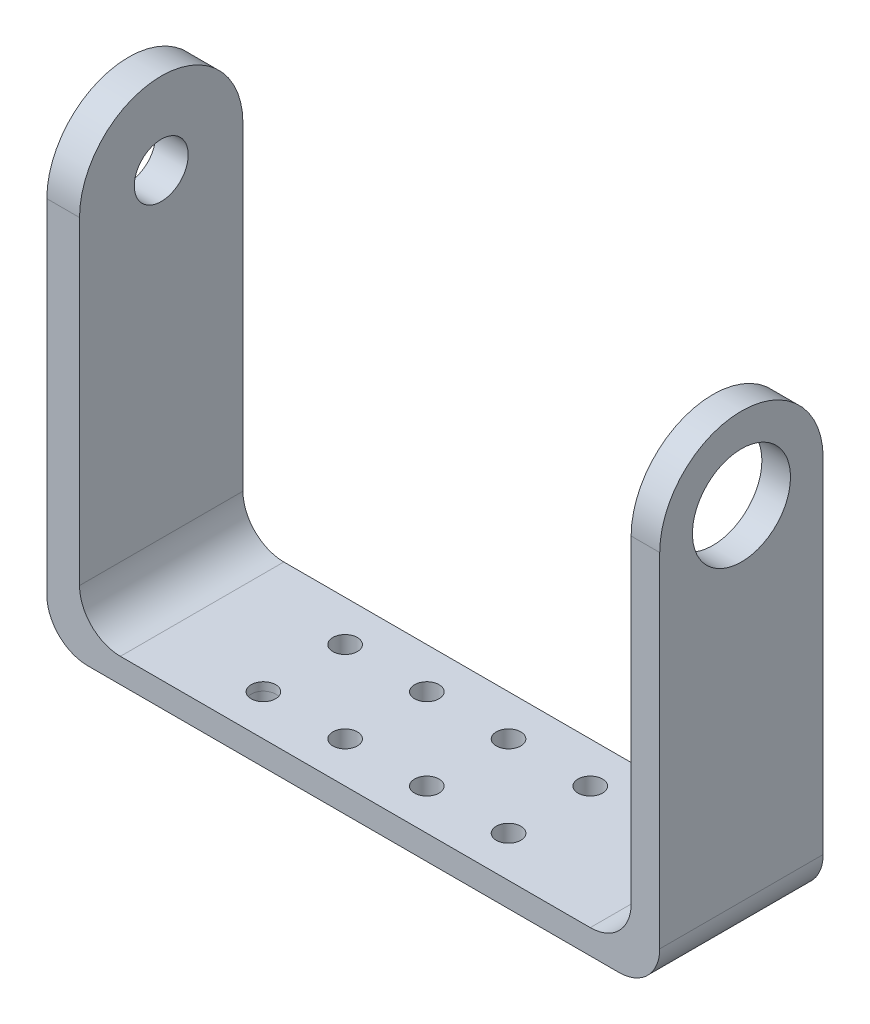
SolidWorks part; units mm, degrees
material "6061 합금"
ref_plane "정면" through (0, 0, 0) normal (0, 0, 1) x (1, 0, 0)
ref_plane "윗면" through (0, 0, 0) normal (0, 1, 0) x (1, 0, 0)
ref_plane "우측면" through (0, 0, 0) normal (1, 0, 0) x (0, 0, -1)
sketch "스케치2" plane through (0, 0, 0) normal (0, 1, 0) x (1, 0, 0)
  line L0 (0, 10) -> (0, -10) construction
  line L1 (35, -10) -> (-35, -10)
  line L3 (35, 10) -> (-35, 10)
  line L4 (-35, -10) -> (-35, 10)
  line L5 (35, -10) -> (-35, 10) construction
  line L6 (35, 10) -> (-35, -10) construction
  line L8 (35, 10) -> (38.5, 10)
  line L10 (35, -10) -> (38.5, -10)
  line L11 (38.5, 10) -> (38.5, -10)
  circle A0 centre (-15, 5) radius 1.5
  circle A1 centre (-5, 5) radius 1.5
  circle A2 centre (-15, -5) radius 1.5
  circle A3 centre (-5, -5) radius 1.5
  circle A4 centre (15, -5) radius 1.5
  circle A5 centre (5, -5) radius 1.5
  circle A6 centre (5, 5) radius 1.5
  circle A7 centre (15, 5) radius 1.5
  point P0 (0, 0)
  point P6 (-15, 5)
  point P7 (-5, 5)
  point P8 (-15, -5)
  point P9 (-5, -5)
  dimension "D9" = 5
  dimension "D1" = 70
  dimension "D2" = 20
  dimension "D3" = 3.5
  dimension "D4" = 5
  dimension "D5" = 10
  dimension "D6" = 5
  dimension "D7" = 10
  dimension "D8" = 10
extrude "보스-돌출1" add sketch "스케치2" along normal blind 2
ref_plane "평면1" through (0, 2, 0) normal (0, 1, 0) x (1, 0, 0)
sketch "스케치3" plane through (0, 2, 0) normal (0, 1, 0) x (1, 0, 0)
  line L0 (-35, -10) -> (38.5, -10) construction
  line L1 (-35, 10) -> (-32.5, 10)
  line L2 (-35, 10) -> (-35, -10)
  line L3 (-35, -10) -> (-32.5, -10)
  line L4 (-32.5, 10) -> (-32.5, -10)
  line L5 (-35, -10) -> (38.5, -10) construction
  line L6 (38.5, 10) -> (35, 10)
  line L7 (38.5, 10) -> (38.5, -10)
  line L8 (38.5, -10) -> (35, -10)
  line L9 (35, 10) -> (35, -10)
  dimension "D1" = 2.5
  dimension "D2" = 3.5
extrude "보스-돌출2" add sketch "스케치3" along normal blind 55
ref_plane "평면2" through (38.5, 0, 0) normal (1, 0, 0) x (0, 0, -1)
ref_plane "평면3" through (-35, 0, 0) normal (-1, 0, 0) x (0, 0, 1)
sketch "스케치9" plane through (38.5, 0, 0) normal (1, 0, 0) x (0, 0, -1)
  line L0 (-10, 57) -> (10, 57) construction
  line L1 (-10, 57) -> (-10, 0) construction
  line L4 (-10, 47) -> (-10, 57)
  line L5 (-10, 57) -> (10, 57)
  line L6 (10, 57) -> (10, 47)
  line L7 (-10, 47) -> (10, 47) construction
  arc A2 (10, 47) -> (-10, 47) centre (0, 47) ccw
  circle A3 centre (0, 47) radius 6
  point P10 (0, 47)
  point P17 (0, 54.07)
  point P18 (-7.07, 47)
  point P19 (0, 47)
  dimension "D6" = 12
  dimension "D4" = 7.07
  dimension "D5" = 7.07
extrude "컷-돌출1" cut sketch "스케치9" against normal blind 87 contours A2 L6 L5 | A2 L5 L4 | L7 A3 | A3 L7
sketch "스케치7" plane through (-35, 0, 0) normal (-1, 0, 0) x (0, 0, 1)
  circle A0 centre (0, 47) radius 6
  circle A1 centre (0, 47) radius 3.3
extrude "보스-돌출3" add sketch "스케치7" against normal blind 2.5
ref_plane "평면4" through (0, 0, 0) normal (0, -1, 0) x (-1, 0, 0)
ref_plane "평면5" through (-35, 0, 0) normal (-1, 0, 0) x (0, 0, 1)
sketch "스케치10" plane through (-35, 0, 0) normal (-1, 0, 0) x (0, 0, 1)
  line L0 (10, 0) -> (-10, 0)
  line L1 (-11, 0) -> (11, 0) construction
  line L2 (10, 47) -> (10, 0) construction
  line L3 (-10, 47) -> (-10, 0) construction
  line L4 (-10, 0) -> (-10, 47)
  line L6 (10, 47) -> (10, 0)
  arc A0 (-10, 47) -> (10, 47) centre (0, 47) cw
  circle A1 centre (0, 47) radius 3.3
extrude "보스-돌출4" add sketch "스케치10" along normal blind 1.5 contours A0 L4 L0 L6 A1
ref_plane "평면6" through (0, 2, 0) normal (0, 1, 0) x (1, 0, 0)
sketch "스케치11" plane through (0, 2, 0) normal (0, 1, 0) x (1, 0, 0)
  line L1 (-32.5, -10) -> (35, -10)
  line L2 (-32.5, -10) -> (-32.5, 10)
  line L3 (-32.5, 10) -> (35, 10)
  line L4 (35, -10) -> (35, 10)
  circle A0 centre (-15, 5) radius 1.5
  circle A1 centre (-5, 5) radius 1.5
  circle A2 centre (5, 5) radius 1.5
  circle A3 centre (15, 5) radius 1.5
  circle A4 centre (15, -5) radius 1.5
  circle A5 centre (5, -5) radius 1.5
  circle A6 centre (-5, -5) radius 1.5
  circle A7 centre (-15, -5) radius 1.4989
  dimension "D1" = 3
extrude "보스-돌출5" add sketch "스케치11" along normal blind 1
fillet "필렛6" radius 5 1 edges at (-32.5, 3, 0)
fillet "필렛7" radius 5 1 edges at (35, 3, 0)
fillet "필렛8" radius 5 2 edges at (38.5, 0, 0) (-36.5, 0, 0)
